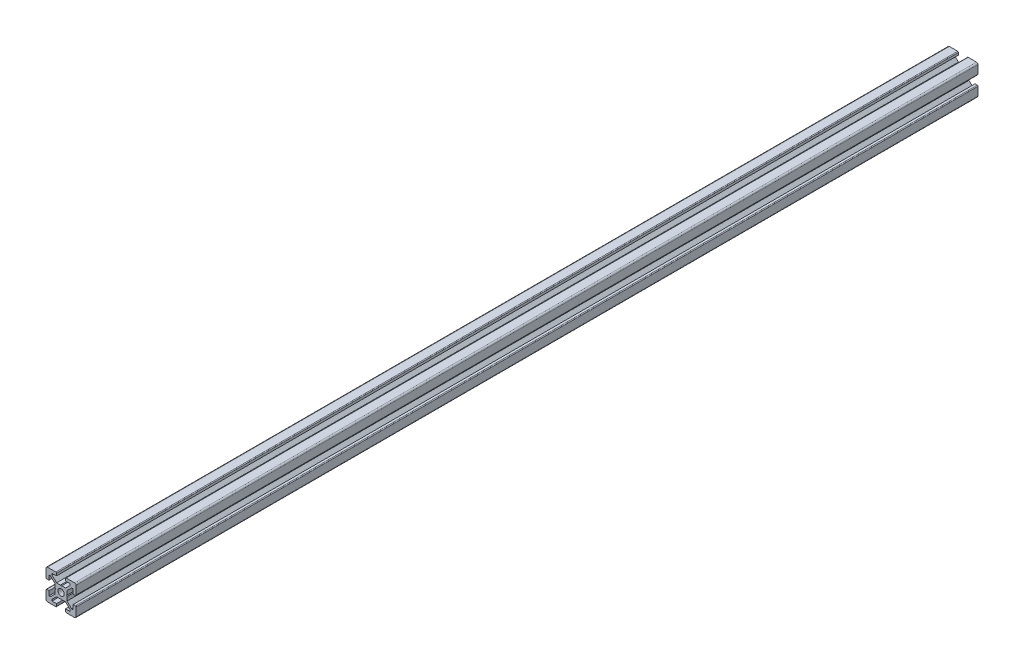
SolidWorks part; units mm, degrees
material "Lega 6061"
ref_plane "Piano frontale" through (0, 0, 0) normal (0, 0, 1) x (1, 0, 0)
ref_plane "Piano superiore" through (0, 0, 0) normal (0, 1, 0) x (1, 0, 0)
ref_plane "Piano destro" through (0, 0, 0) normal (1, 0, 0) x (0, 0, -1)
sketch "Schizzo1" plane through (0, 0, 0) normal (0, 0, 1) x (1, 0, 0)
  line L0 (0, 0) -> (-10, 0) construction
  line L1 (0, 0) -> (0, 10) construction
  line L2 (-3.6, 0) -> (-4, 0.4)
  line L3 (-4, 0.4) -> (-4, 3)
  line L4 (-4, 3) -> (-7, 6)
  line L5 (-7, 6) -> (-8, 6)
  line L6 (-8, 6) -> (-8, 3)
  line L7 (-8, 3) -> (-9.5, 3)
  line L8 (-10, 3.5) -> (-10, 9)
  line L9 (0, 0) -> (-10, 10) construction
  line L10 (0, 3.6) -> (-0.4, 4)
  line L11 (-0.4, 4) -> (-3, 4)
  line L12 (-3, 4) -> (-6, 7)
  line L13 (-6, 7) -> (-6, 8)
  line L14 (-6, 8) -> (-3, 8)
  line L15 (-3, 8) -> (-3, 9.5)
  line L16 (-3.5, 10) -> (-9, 10)
  line L17 (0, 0) -> (-10, -10) construction
  line L18 (-3.5, -10) -> (-9, -10)
  line L19 (-3, -8) -> (-3, -9.5)
  line L20 (-6, -8) -> (-3, -8)
  line L21 (-6, -7) -> (-6, -8)
  line L22 (-3, -4) -> (-6, -7)
  line L23 (-0.4, -4) -> (-3, -4)
  line L24 (0, -3.6) -> (-0.4, -4)
  line L25 (-10, -3.5) -> (-10, -9)
  line L26 (-8, -3) -> (-9.5, -3)
  line L27 (-8, -6) -> (-8, -3)
  line L28 (-7, -6) -> (-8, -6)
  line L29 (-4, -3) -> (-7, -6)
  line L30 (-4, -0.4) -> (-4, -3)
  line L31 (-3.6, 0) -> (-4, -0.4)
  line L32 (0, 0) -> (10, -10) construction
  line L33 (0, 0) -> (10, 10) construction
  line L34 (3.6, 0) -> (4, -0.4)
  line L35 (4, -0.4) -> (4, -3)
  line L36 (4, -3) -> (7, -6)
  line L37 (7, -6) -> (8, -6)
  line L38 (8, -6) -> (8, -3)
  line L39 (8, -3) -> (9.5, -3)
  line L40 (10, -3.5) -> (10, -9)
  line L41 (0, -3.6) -> (0.4, -4)
  line L42 (0.4, -4) -> (3, -4)
  line L43 (3, -4) -> (6, -7)
  line L44 (6, -7) -> (6, -8)
  line L45 (6, -8) -> (3, -8)
  line L46 (3, -8) -> (3, -9.5)
  line L47 (3.5, -10) -> (9, -10)
  line L48 (3.5, 10) -> (9, 10)
  line L49 (3, 8) -> (3, 9.5)
  line L50 (6, 8) -> (3, 8)
  line L51 (6, 7) -> (6, 8)
  line L52 (3, 4) -> (6, 7)
  line L53 (0.4, 4) -> (3, 4)
  line L54 (0, 3.6) -> (0.4, 4)
  line L55 (10, 3.5) -> (10, 9)
  line L56 (8, 3) -> (9.5, 3)
  line L57 (8, 6) -> (8, 3)
  line L58 (7, 6) -> (8, 6)
  line L59 (4, 3) -> (7, 6)
  line L60 (4, 0.4) -> (4, 3)
  line L61 (3.6, 0) -> (4, 0.4)
  arc A0 (-10, 9) -> (-9, 10) centre (-9, 9) cw
  arc A1 (-3, 9.5) -> (-3.5, 10) centre (-3.5, 9.5) ccw
  arc A2 (-9.5, 3) -> (-10, 3.5) centre (-9.5, 3.5) cw
  arc A3 (-9.5, -3) -> (-10, -3.5) centre (-9.5, -3.5) ccw
  arc A4 (-3, -9.5) -> (-3.5, -10) centre (-3.5, -9.5) cw
  arc A5 (-10, -9) -> (-9, -10) centre (-9, -9) ccw
  arc A6 (10, -9) -> (9, -10) centre (9, -9) cw
  arc A7 (3, -9.5) -> (3.5, -10) centre (3.5, -9.5) ccw
  arc A8 (9.5, -3) -> (10, -3.5) centre (9.5, -3.5) cw
  arc A9 (9.5, 3) -> (10, 3.5) centre (9.5, 3.5) ccw
  arc A10 (3, 9.5) -> (3.5, 10) centre (3.5, 9.5) cw
  arc A11 (10, 9) -> (9, 10) centre (9, 9) ccw
  circle A12 centre (0, 0) radius 2.1
  point P24 (-3, 10)
  point P27 (-10, 3)
  point P49 (-10, -3)
  point P50 (-3, -10)
  point P92 (3, -10)
  point P93 (10, -3)
  point P94 (10, 3)
  point P95 (3, 10)
  dimension "D2" = 1
  dimension "D12" = 0.5
  dimension "D13" = 4.2
  dimension "D3" = 8
  dimension "D4" = 0.4
  dimension "D5" = 45
  dimension "D6" = 6
  dimension "D7" = 12
  dimension "D8" = 20
  dimension "D9" = 2
  dimension "D10" = 4
  dimension "D11" = 45
extrude "Estrusione-Estrusione1" add sketch "Schizzo1" along normal blind 600
